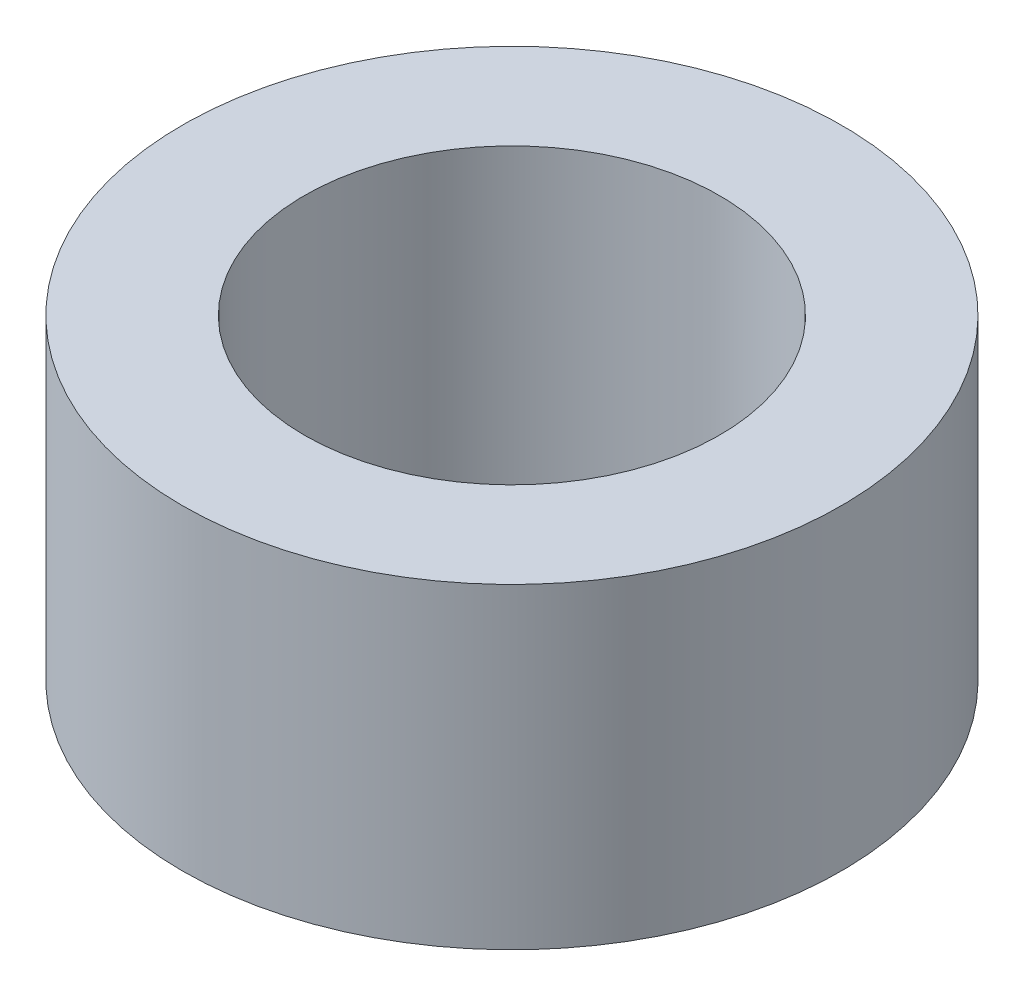
SolidWorks part; units mm, degrees
material "6061-T6 (SS)"
ref_plane "X-Y Datum" through (0, 0, 0) normal (0, 0, 1) x (1, 0, 0)
ref_plane "X-Z Datum" through (0, 0, 0) normal (0, 1, 0) x (1, 0, 0)
ref_plane "Y-Z Datum" through (0, 0, 0) normal (1, 0, 0) x (0, 0, -1)
sketch "Sketch1" plane through (0, 0, 0) normal (0, 1, 0) x (1, 0, 0)
  circle A0 centre (0, 0) radius 2
  circle A1 centre (0, 0) radius 3.175
  dimension "D1" = 4
  dimension "D2" = 6.35
extrude "Boss-Extrude1" add sketch "Sketch1" against normal blind 3.048
